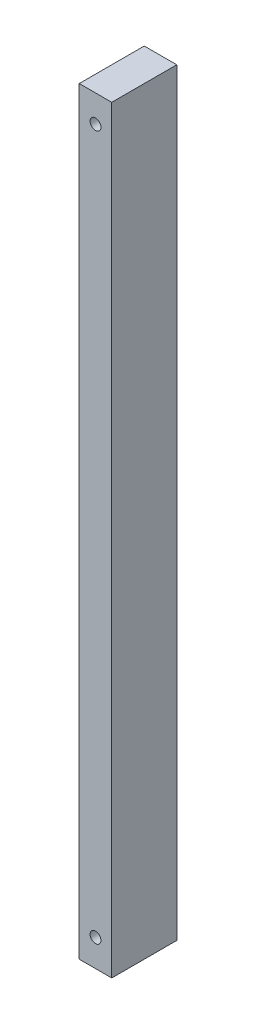
SolidWorks part; units mm, degrees
material "Pine"
ref_plane "Front Plane" through (0, 0, 0) normal (0, 0, 1) x (1, 0, 0)
ref_plane "Top Plane" through (0, 0, 0) normal (0, 1, 0) x (1, 0, 0)
ref_plane "Right Plane" through (0, 0, 0) normal (1, 0, 0) x (0, 0, -1)
sketch "Sketch1" plane through (0, 0, 0) normal (1, 0, 0) x (0, 0, -1)
  line L1 (0, 0) -> (38.1, 0)
  line L2 (0, 0) -> (0, 444.5)
  line L3 (0, 444.5) -> (38.1, 444.5)
  line L4 (38.1, 0) -> (38.1, 444.5)
  dimension "D1" = 444.5
  dimension "D2" = 38.1
extrude "Boss-Extrude1" add sketch "Sketch1" along normal blind 19.05
sketch "Sketch2" plane through (0, 0, 0) normal (0, 0, 1) x (1, 0, 0)
  line L0 (9.525, 444.5) -> (9.525, 0) construction
  line L1 (19.05, 444.5) -> (0, 444.5) construction
  line L2 (19.05, 0) -> (0, 0) construction
  circle A0 centre (9.525, 15.875) radius 3.175
  circle A1 centre (9.525, 428.625) radius 3.175
  dimension "D2" = 6.35
  dimension "D4" = 6.35
  dimension "D1" = 15.875
  dimension "D3" = 15.875
extrude "Cut-Extrude1" cut sketch "Sketch2" against normal through all
